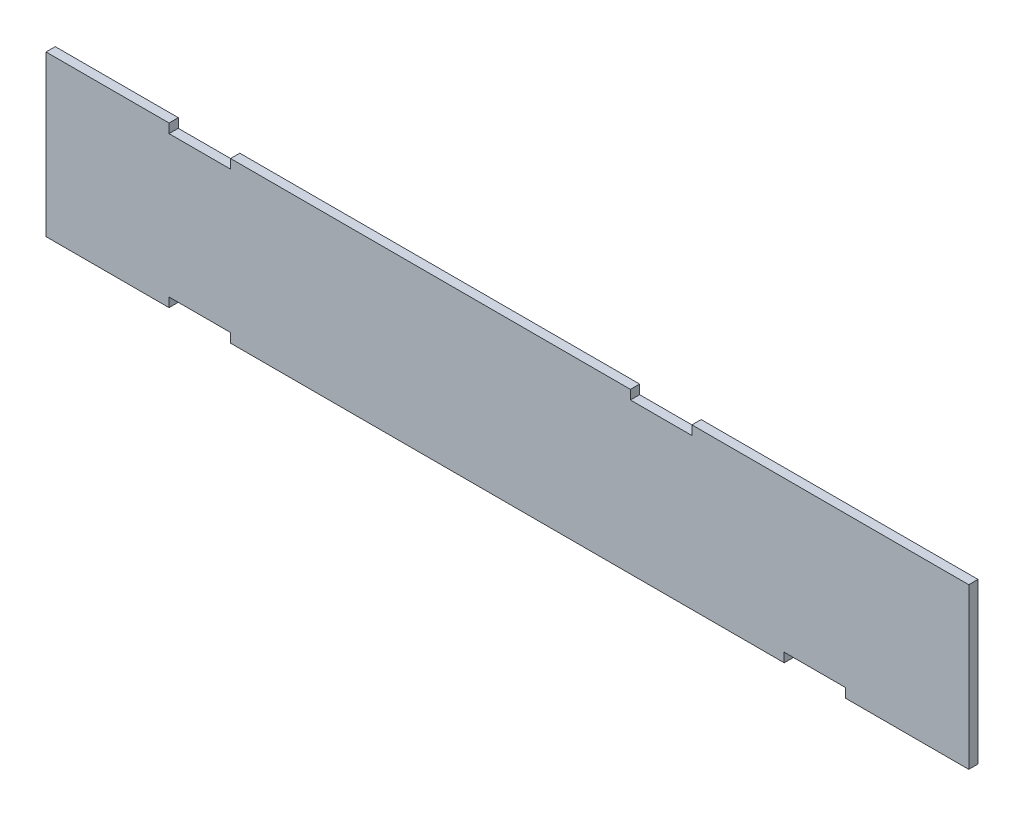
SolidWorks part; units mm, degrees
ref_plane "Front Plane" through (0, 0, 0) normal (0, 0, 1) x (1, 0, 0)
ref_plane "Top Plane" through (0, 0, 0) normal (0, 1, 0) x (1, 0, 0)
ref_plane "Right Plane" through (0, 0, 0) normal (1, 0, 0) x (0, 0, -1)
sketch "Sketch1" plane through (0, 0, 0) normal (0, 0, 1) x (1, 0, 0)
  line L1 (150, -26) -> (-150, -26)
  line L2 (150, -26) -> (150, 26)
  line L3 (150, 26) -> (-150, 26)
  line L4 (-150, -26) -> (-150, 26)
  line L5 (150, -26) -> (-150, 26) construction
  line L6 (150, 26) -> (-150, -26) construction
  point P0 (0, 0)
  dimension "D1" = 300
  dimension "D2" = 52
extrude "Boss-Extrude2" add sketch "Sketch1" along normal blind 3
sketch "Sketch2" plane through (0, 0, 3) normal (0, 0, 1) x (1, 0, 0)
  line L0 (-110, 26) -> (-110, 23)
  line L1 (150, 26) -> (-150, 26) construction
  line L2 (-110, 23) -> (-90, 23)
  line L3 (-90, 23) -> (-90, 26)
  line L4 (-150, 26) -> (-150, -26) construction
  line L5 (-90, 26) -> (-110, 26)
  dimension "D1" = 3
  dimension "D2" = 40
  dimension "D3" = 20
extrude "Cut-Extrude1" cut sketch "Sketch2" against normal blind 10
sketch "Sketch3" plane through (0, 0, 3) normal (0, 0, 1) x (1, 0, 0)
  line L0 (-110, -26) -> (-110, -23)
  line L1 (-150, -26) -> (150, -26) construction
  line L2 (-110, -23) -> (-90, -23)
  line L3 (-90, -23) -> (-90, -26)
  line L4 (-110, -26) -> (-90, -26)
  line L5 (90, -26) -> (90, -23)
  line L6 (90, -23) -> (110, -23)
  line L7 (-150, 26) -> (-150, -26) construction
  line L8 (110, -23) -> (110, -26)
  line L9 (90, -26) -> (110, -26)
  dimension "D1" = 20
  dimension "D2" = 3
  dimension "D3" = 40
  dimension "D4" = 20
  dimension "D5" = 3
  dimension "D6" = 180
extrude "Cut-Extrude4" cut sketch "Sketch3" against normal blind 10
sketch "Sketch4" plane through (0, 0, 3) normal (0, 0, 1) x (1, 0, 0)
  line L0 (40, 26) -> (40, 23)
  line L1 (150, 26) -> (-90, 26) construction
  line L2 (40, 23) -> (60, 23)
  line L3 (60, 23) -> (60, 26)
  line L4 (-90, 23) -> (-90, 26) construction
  line L5 (60, 26) -> (40, 26)
  dimension "D1" = 20
  dimension "D2" = 130
  dimension "D3" = 3
extrude "Cut-Extrude5" cut sketch "Sketch4" against normal blind 10
